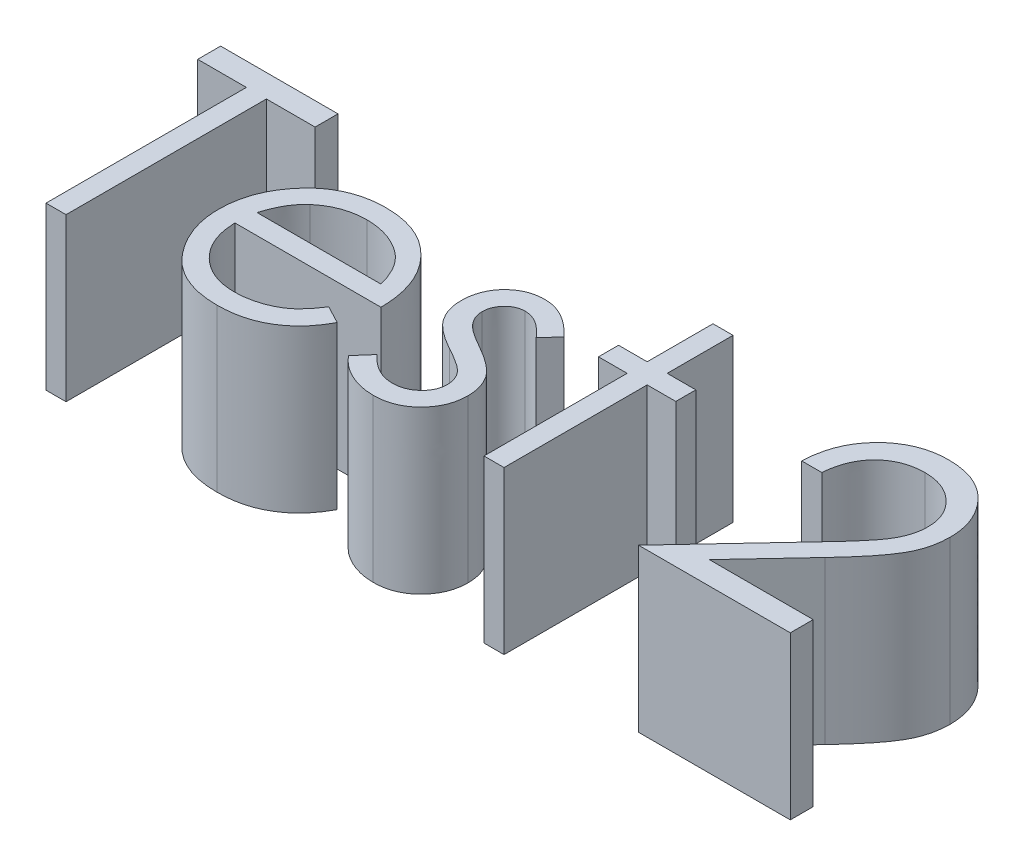
SolidWorks part; units mm, degrees
ref_plane "Front Plane" through (0, 0, 0) normal (0, 0, 1) x (1, 0, 0)
ref_plane "Top Plane" through (0, 0, 0) normal (0, 1, 0) x (1, 0, 0)
ref_plane "Right Plane" through (0, 0, 0) normal (1, 0, 0) x (0, 0, -1)
sketch "Sketch2" plane through (0, 0, 0) normal (0, 1, 0) x (1, 0, 0)
  line L0 (0, 0) -> (43.4315, 0) construction
  text T0 "Test 2\r\n"
  point P2 (5.1868, 2.31)
  point P4 (1.5032, 0)
  point P5 (-4.8699, 0)
extrude "Boss-Extrude1" add sketch "Sketch2" along normal blind 2.54
